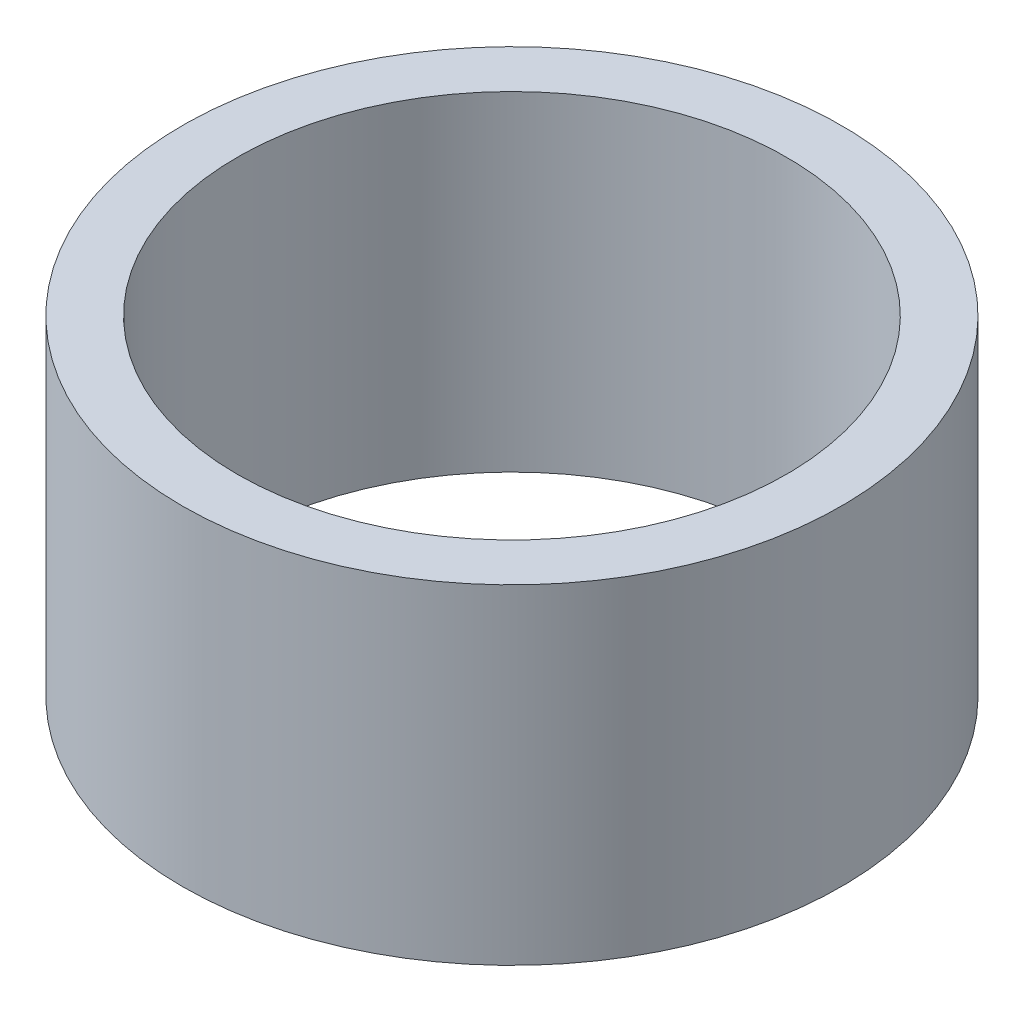
SolidWorks part; units mm, degrees
ref_plane "Front Plane" through (0, 0, 0) normal (0, 0, 1) x (1, 0, 0)
ref_plane "Top Plane" through (0, 0, 0) normal (0, 1, 0) x (1, 0, 0)
ref_plane "Right Plane" through (0, 0, 0) normal (1, 0, 0) x (0, 0, -1)
sketch "Sketch1" plane through (0, 0, 0) normal (0, 1, 0) x (1, 0, 0)
  circle A0 centre (0, 0) radius 6
  circle A1 centre (0, 0) radius 5
extrude "Boss-Extrude1" add sketch "Sketch1" along normal blind 6
